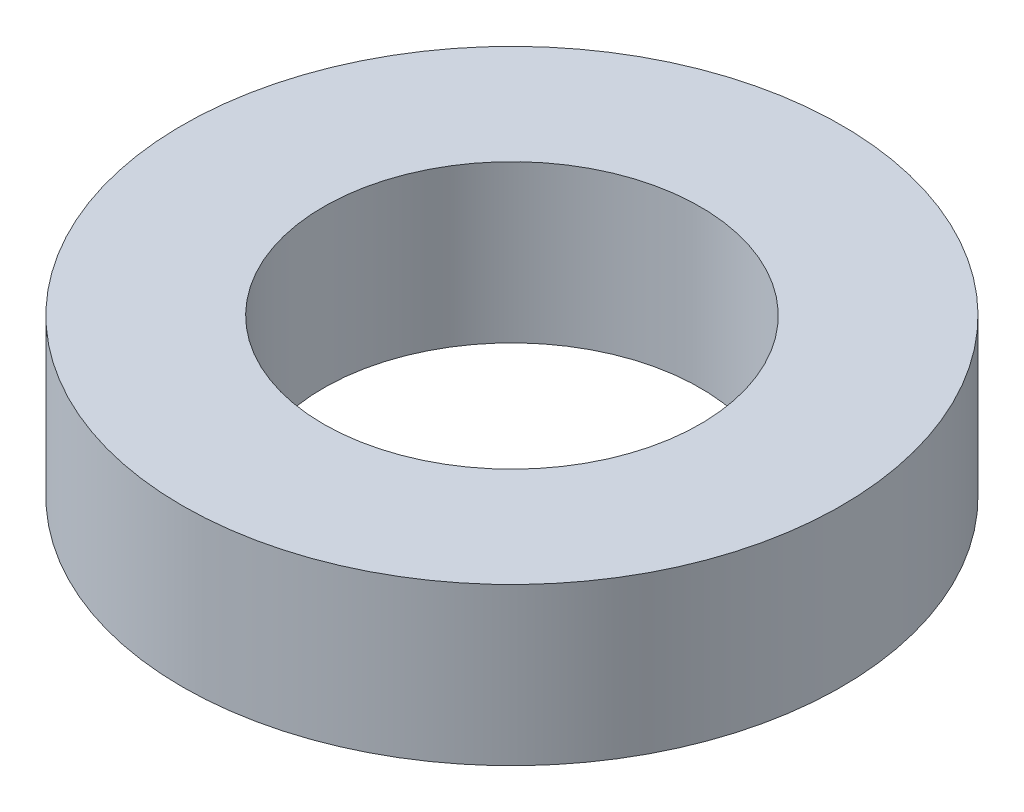
SolidWorks part; units mm, degrees
material "1023 Carbon Steel Sheet (SS)"
ref_plane "Front Plane" through (0, 0, 0) normal (0, 0, 1) x (1, 0, 0)
ref_plane "Top Plane" through (0, 0, 0) normal (0, 1, 0) x (1, 0, 0)
ref_plane "Right Plane" through (0, 0, 0) normal (1, 0, 0) x (0, 0, -1)
ref_axis "Axis1" through (0, 55, 0) along (0, -1, 0)
sketch "Sketch1" plane through (0, 0, 0) normal (0, 0, 1) x (1, 0, 0)
  line L0 (0, 55) -> (0, -55) construction
  line L1 (-10.5, -2.5) -> (-6, -2.5)
  line L2 (-10.5, -2.5) -> (-10.5, 2.5)
  line L3 (-10.5, 2.5) -> (-6, 2.5)
  line L4 (-6, -2.5) -> (-6, 2.5)
  line L5 (-10.5, -2.5) -> (-6, 2.5) construction
  line L6 (-10.5, 2.5) -> (-6, -2.5) construction
  line L7 (0, 0) -> (0, 24.718) construction
  point P0 (-8.25, 0)
  point P10 (0, 0)
  dimension "D1" = 12
  dimension "D2" = 21
  dimension "D3" = 5
revolve "Revolve1" add sketch "Sketch1" angle 360 about axis through (0, 55, 0) along (0, -1, 0)
